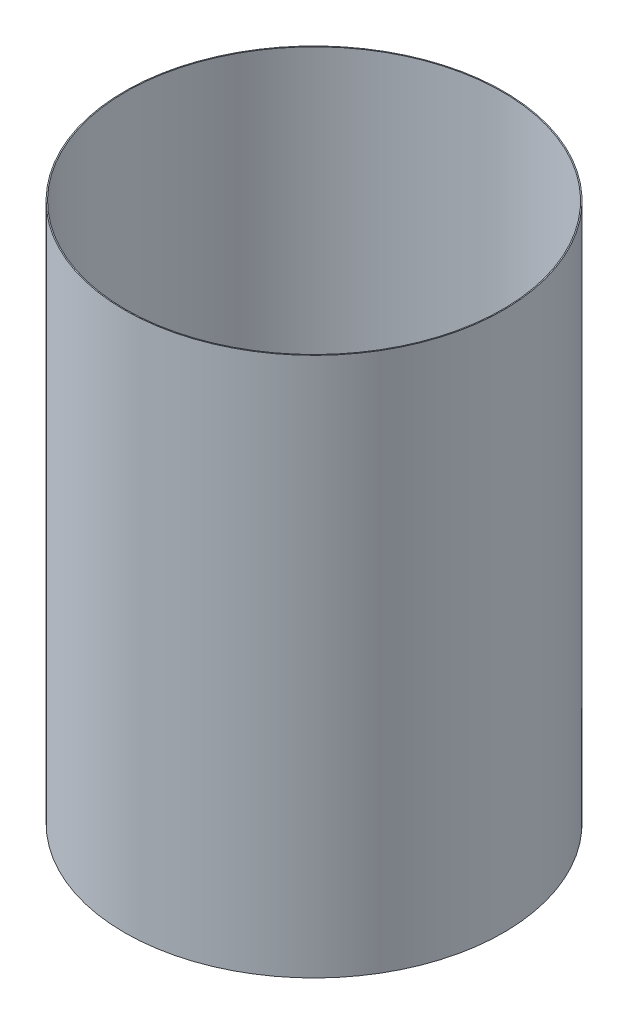
SolidWorks part; units mm, degrees
material "Thornel Mat VMA"
ref_plane "Front Plane" through (0, 0, 0) normal (0, 0, 1) x (1, 0, 0)
ref_plane "Top Plane" through (0, 0, 0) normal (0, 1, 0) x (1, 0, 0)
ref_plane "Right Plane" through (0, 0, 0) normal (1, 0, 0) x (0, 0, -1)
ref_axis "Axis1" through (0, 55, 0) along (0, -1, 0)
sketch "Sketch1" plane through (0, 0, 0) normal (0, 0, 1) x (1, 0, 0)
  line L0 (-46.609, -19.9059) -> (-46.609, -153.2559)
  line L2 (-38.1, -19.9059) -> (0, -19.9059) construction
  line L3 (-38.1, -153.2559) -> (0, -153.2559) construction
  point P2 (-46.609, -19.9059)
revolve "Revolve-Thin1" add sketch "Sketch1" angle 360 about axis through (0, 55, 0) along (0, -1, 0)
equation "\"D3@Revolve-Thin1\"=\"CF THICKNESS@Cryo Tank.Assembly\""
